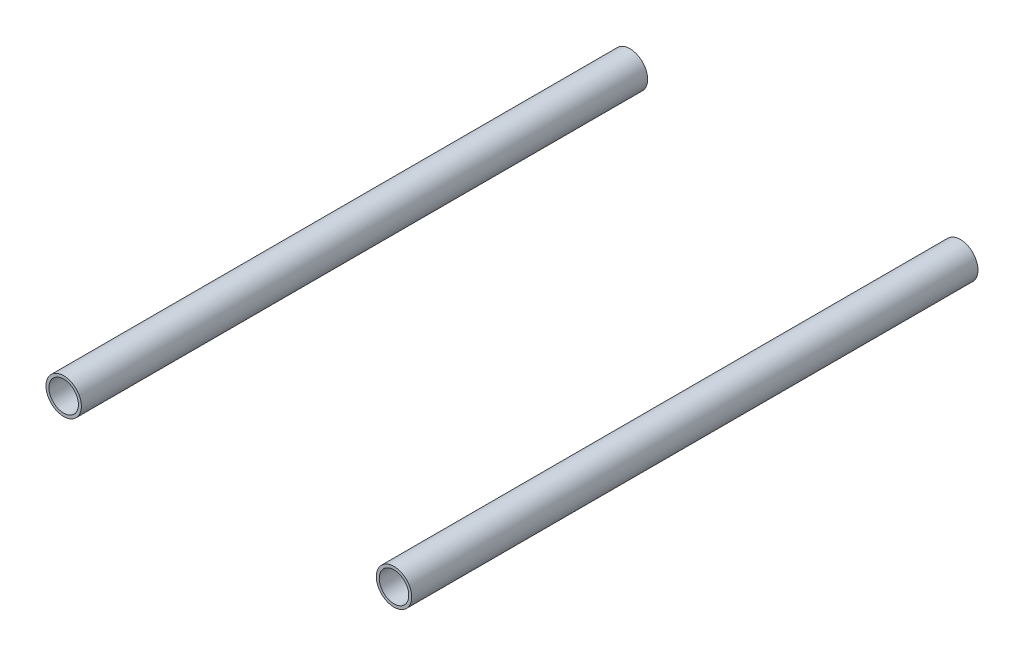
SolidWorks part; units mm, degrees
material "Carbon Fibre"
ref_plane "Front Plane" through (0, 0, 0) normal (0, 0, 1) x (1, 0, 0)
ref_plane "Top Plane" through (0, 0, 0) normal (0, 1, 0) x (1, 0, 0)
ref_plane "Right Plane" through (0, 0, 0) normal (1, 0, 0) x (0, 0, -1)
sketch "Sketch1" plane through (0, 0, 0) normal (0, 0, 1) x (1, 0, 0)
  circle A0 centre (0, 0) radius 9.525
  circle A1 centre (177.8, 0) radius 9.525
  circle A2 centre (0, 0) radius 7.9375
  circle A3 centre (177.8, 0) radius 7.9375
  dimension "D1" = 19.05
  dimension "D4" = 1.5875
  dimension "D3" = 177.8
extrude "Boss-Extrude1" add sketch "Sketch1" along normal mid plane 304.8 contours A0 | A1
